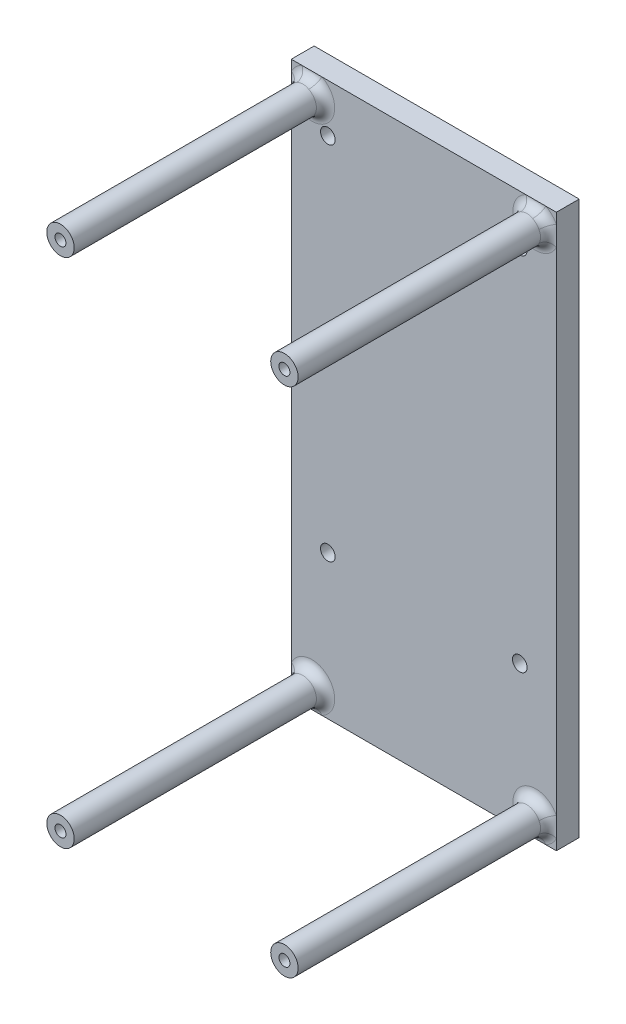
SolidWorks part; units mm, degrees
ref_plane "Piano frontale" through (0, 0, 0) normal (0, 0, 1) x (1, 0, 0)
ref_plane "Piano superiore" through (0, 0, 0) normal (0, 1, 0) x (1, 0, 0)
ref_plane "Piano destro" through (0, 0, 0) normal (1, 0, 0) x (0, 0, -1)
sketch "Schizzo1" plane through (0, 0, 0) normal (0, 0, 1) x (1, 0, 0)
  line L0 (86.8365, -133.8804) -> (86.8365, -12.8804)
  line L1 (86.8365, -12.8804) -> (144.8365, -12.8804)
  line L2 (144.8365, -12.8804) -> (144.8365, -133.8804)
  line L3 (144.8365, -133.8804) -> (86.8365, -133.8804)
  line L4 (144.8365, -133.8804) -> (86.8365, -12.8804) construction
  line L5 (86.8365, -133.8804) -> (144.8365, -12.8804) construction
  point P2 (115.8365, -73.3804)
  point P3 (115.8365, -73.3804)
  dimension "D1" = 121
  dimension "D2" = 58
extrude "Estrusione-Estrusione2" add sketch "Schizzo1" along normal blind 5
sketch "Schizzo12" plane through (0, 0, 0) normal (0, 0, -1) x (-1, 0, 0)
  line L0 (-115.8365, -24.133) -> (-115.8365, -99.1285) construction
  line L1 (-144.8365, -133.8804) -> (-144.8365, -12.8804) construction
  line L2 (-86.8365, -12.8804) -> (-86.8365, -133.8804) construction
  line L3 (-129.4279, -62.8804) -> (-96.5442, -62.8804) construction
  line L5 (-144.8365, -12.8804) -> (-86.8365, -12.8804) construction
  circle A0 centre (-94.8365, -102.3804) radius 1.6
  circle A1 centre (-136.8365, -102.3804) radius 1.6
  circle A2 centre (-136.8365, -23.3804) radius 1.6
  circle A3 centre (-94.8365, -23.3804) radius 1.6
  dimension "D4" = 3.2
  dimension "D1" = 10.5
  dimension "D2" = 79
  dimension "D3" = 42
extrude "Taglio-Estrusione1" cut sketch "Schizzo12" against normal up to next
sketch "Schizzo2" plane through (0, 0, 5) normal (0, 0, 1) x (1, 0, 0)
  line L0 (115.8365, -12.8804) -> (115.8365, -133.8804) construction
  line L1 (144.8365, -12.8804) -> (86.8365, -12.8804) construction
  line L2 (86.8365, -133.8804) -> (144.8365, -133.8804) construction
  line L3 (144.8365, -73.3804) -> (86.8365, -73.3804) construction
  line L4 (144.8365, -133.8804) -> (144.8365, -12.8804) construction
  line L5 (86.8365, -12.8804) -> (86.8365, -133.8804) construction
  circle A2 centre (140.3365, -129.3804) radius 3
  circle A3 centre (91.3365, -129.3804) radius 3
  circle A4 centre (140.3365, -17.3804) radius 3
  circle A5 centre (91.3365, -17.3804) radius 3
  dimension "D1" = 6
  dimension "D2" = 49
  dimension "D3" = 112
extrude "Estrusione-Estrusione3" add sketch "Schizzo2" along normal blind 55
ref_plane "Piano2" through (87.9968, 0, 0) normal (1, 0, 0) x (0, 1, 0)
ref_plane "Piano4" through (64.5561, 31.5493, 0) normal (0.8984, 0.4391, 0) x (0.4391, -0.8984, 0)
fillet "Raccordo1" radius 2 4 edges at (88.3365, -17.3804, 5) (137.3365, -17.3804, 5) (137.3365, -129.3804, 5) (88.3365, -129.3804, 5)
hole_wizard "Foro per Vite M3-1" positions "Schizzo14" profile "Schizzo15" hole size "M3" standard "ISO"
sketch "Schizzo14" plane through (0, 0, 60) normal (0, 0, 1) x (1, 0, 0)
  circle A0 centre (140.3365, -129.3804) radius 3 construction
  point P0 (140.3365, -129.3804)
  point P2 (91.3365, -129.3804)
  point P5 (91.3365, -17.3804)
  point P8 (140.3365, -17.3804)
sketch "Schizzo15" plane through (140.3365, -129.3804, 60) normal (1, 0, 0) x (0, -1, 0)
  line L0 (0, 0) -> (0, 20.721)
  line L1 (0, 20.721) -> (1.2, 20)
  line L2 (1.2, 20) -> (1.2, 0)
  line L5 (1.2, 0) -> (0, 0)
  line L10 (0, 20.721) -> (-1.2, 20) construction
  line L11 (0, -6.35) -> (0, 107.95) construction
  dimension "Hole Dia." = 2.4
  dimension "Hole Depth" = 20
  dimension "Drill Angle" = 118
